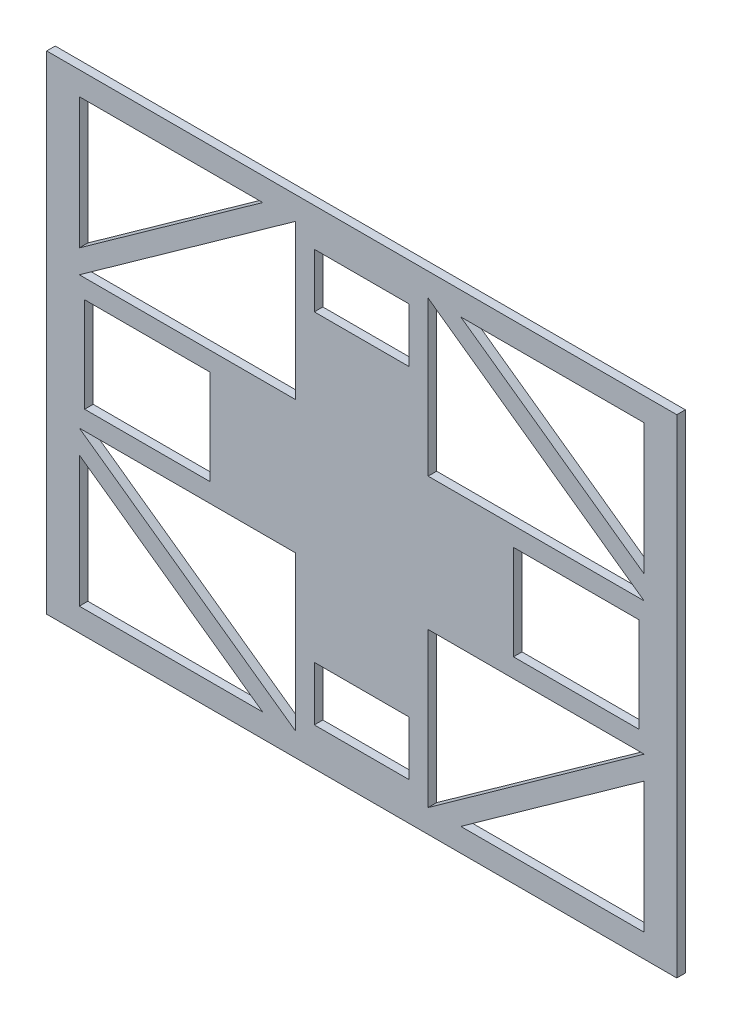
SolidWorks part; units mm, degrees
material "CA"
ref_plane "Ön Düzlem" through (0, 0, 0) normal (0, 0, 1) x (1, 0, 0)
ref_plane "Üst Düzlem" through (0, 0, 0) normal (0, 1, 0) x (1, 0, 0)
ref_plane "Sağ Düzlem" through (0, 0, 0) normal (1, 0, 0) x (0, 0, -1)
sketch "Çizim1" plane through (0, 0, 0) normal (0, 0, 1) x (1, 0, 0)
  line L0 (-35, 128.6) -> (-166.1, 35)
  line L1 (-166.1, -35) -> (166.1, -35)
  line L2 (-166.1, -35) -> (-166.1, 35)
  line L3 (-166.1, 35) -> (166.1, 35)
  line L4 (166.1, -35) -> (166.1, 35)
  line L5 (-166.1, -35) -> (166.1, 35) construction
  line L6 (-166.1, 35) -> (166.1, -35) construction
  line L7 (-35, -128.6) -> (35, -128.6)
  line L8 (-35, -128.6) -> (-35, 128.6)
  line L9 (-35, 128.6) -> (35, 128.6)
  line L10 (35, -128.6) -> (35, 128.6)
  line L11 (-35, -128.6) -> (35, 128.6) construction
  line L12 (-35, 128.6) -> (35, -128.6) construction
  line L13 (-35, -128.6) -> (-166.1, -35)
  line L14 (35, -128.6) -> (166.1, -35)
  line L15 (166.1, 35) -> (35, 128.6)
  line L16 (-148.8901, 35) -> (-35, 116.3129)
  line L17 (-35, -116.3129) -> (-148.8901, -35)
  line L18 (35, -116.3129) -> (148.8901, -35)
  line L19 (35, 116.3129) -> (148.8901, 35)
  line L20 (-35, 25) -> (-146.1, 25)
  line L21 (-146.1, 25) -> (-146.1, -25)
  line L22 (-146.1, -25) -> (-35, -25)
  line L23 (35, 25) -> (146.1, 25)
  line L24 (-25, -25) -> (25, -25)
  line L25 (-25, -25) -> (-25, 25)
  line L26 (-25, 25) -> (25, 25)
  line L27 (25, -25) -> (25, 25)
  line L28 (-25, -25) -> (25, 25) construction
  line L29 (-25, 25) -> (25, -25) construction
  line L30 (146.1, 25) -> (146.1, -25)
  line L31 (146.1, -25) -> (35, -25)
  line L32 (-25, 35) -> (-25, 108.6)
  line L33 (-25, 108.6) -> (25, 108.6)
  line L34 (25, 108.6) -> (25, 35)
  line L35 (-25, -35) -> (-25, -108.6)
  line L36 (-25, -108.6) -> (25, -108.6)
  line L37 (25, -108.6) -> (25, -35)
  line L38 (-166.1, -35) -> (-166.1, -128.6)
  line L39 (-166.1, -128.6) -> (-35, -128.6)
  line L40 (-148.8901, -35) -> (-148.8901, -116.3129)
  line L41 (-148.8901, -116.3129) -> (-35, -116.3129)
  line L42 (166.1, -35) -> (166.1, -128.6)
  line L43 (166.1, -128.6) -> (35, -128.6)
  line L44 (35, -116.3129) -> (148.8901, -116.3129)
  line L45 (148.8901, -116.3129) -> (148.8901, -35)
  line L48 (35, 128.6) -> (166.1, 128.6)
  line L49 (166.1, 128.6) -> (166.1, 35)
  line L50 (-166.1, 35) -> (-166.1, 128.6)
  line L51 (-166.1, 128.6) -> (-35, 128.6)
  line L52 (-148.8901, 35) -> (-148.8901, 116.3129)
  line L53 (-148.8901, 116.3129) -> (-35, 116.3129)
  line L54 (-25, -80) -> (25, -80)
  line L55 (-80, 25) -> (-80, -25)
  line L56 (-25, 80) -> (25, 80)
  line L57 (80, 25) -> (80, -25)
  line L58 (35, 116.3129) -> (148.8901, 116.3129)
  line L59 (148.8901, 116.3129) -> (148.8901, 35)
  point P0 (0, 0)
  point P6 (0, 0)
  point P21 (0, 0)
  dimension "D1" = 70
  dimension "D2" = 332.2
  dimension "D3" = 70
  dimension "D4" = 257.2
  dimension "D5" = 10
  dimension "D6" = 10
  dimension "D7" = 10
  dimension "D8" = 10
  dimension "D9" = 20
  dimension "D10" = 10
  dimension "D11" = 10
  dimension "D12" = 10
  dimension "D13" = 10
  dimension "D14" = 20
  dimension "D15" = 20
  dimension "D16" = 20
  dimension "D17" = 80
  dimension "D18" = 80
  dimension "D19" = 80
  dimension "D20" = 80
extrude "Yükseklik-Ekstrüzyon2" add sketch "Çizim1" against normal blind 4.5
sketch "Çizim2" plane through (0, 0, -4.5) normal (0, 0, -1) x (-1, 0, 0)
  circle A0 centre (0, 0) radius 3
  dimension "D1" = 6
extrude "Yükseklik-Ekstrüzyon3" add sketch "Çizim2" along normal blind 10
sketch "Çizim3" plane through (0, 0, 0) normal (0, 0, 1) x (1, 0, 0)
  line L0 (-166.1, 128.6) -> (166.1, 128.6) construction
  line L1 (-166.1, 128.6) -> (-166.1, -128.6) construction
  line L2 (-166.1, -128.6) -> (166.1, -128.6) construction
  line L4 (161.1, 0) -> (166.1, 0) construction
  line L5 (166.1, -128.6) -> (166.1, 128.6) construction
  line L6 (161.1, 25) -> (166.1, 25)
  line L7 (161.1, -25) -> (166.1, -25)
  line L8 (-161.1, -123.6) -> (161.1, -123.6)
  line L9 (161.1, -123.6) -> (161.1, 123.6)
  line L10 (161.1, 123.6) -> (-161.1, 123.6)
  line L11 (-161.1, 123.6) -> (-161.1, -123.6)
  line L12 (-161.1, -123.6) -> (161.1, -123.6)
  line L13 (161.1, -123.6) -> (161.1, 123.6)
  line L14 (161.1, 123.6) -> (-161.1, 123.6)
  line L15 (-161.1, 123.6) -> (-161.1, -123.6)
  circle A0 centre (164.1, 126.6) radius 1
  circle A1 centre (-164.1, 126.6) radius 1
  circle A2 centre (-164.1, -126.6) radius 1
  circle A3 centre (164.1, -126.6) radius 1
  dimension "D4" = 2
  dimension "D5" = 2
  dimension "D7" = 2
  dimension "D10" = 2
  dimension "D13" = 2
  dimension "D2" = 25
  dimension "D3" = 25
  dimension "D6" = 2
  dimension "D8" = 2
  dimension "D9" = 2
  dimension "D11" = 2
  dimension "D12" = 2
  dimension "D14" = 2
  dimension "D15" = 2
  dimension "D1" = 5
sketch "Çizim4" plane through (0, 0, -4.5) normal (0, 0, -1) x (-1, 0, 0)
  line L1 (-52.5, -2.5) -> (-67.5, -2.5)
  line L2 (-52.5, -2.5) -> (-52.5, 2.5)
  line L3 (-52.5, 2.5) -> (-67.5, 2.5)
  line L4 (-67.5, -2.5) -> (-67.5, 2.5)
  line L5 (-52.5, -2.5) -> (-67.5, 2.5) construction
  line L6 (-52.5, 2.5) -> (-67.5, -2.5) construction
  line L7 (2.5, -67.5) -> (-2.5, -67.5)
  line L8 (2.5, -67.5) -> (2.5, -52.5)
  line L9 (2.5, -52.5) -> (-2.5, -52.5)
  line L10 (-2.5, -67.5) -> (-2.5, -52.5)
  line L11 (2.5, -67.5) -> (-2.5, -52.5) construction
  line L12 (2.5, -52.5) -> (-2.5, -67.5) construction
  point P0 (-60, 0)
  point P8 (0, -60)
  dimension "D1" = 5
  dimension "D2" = 15
  dimension "D3" = 60
  dimension "D4" = 5
  dimension "D5" = 15
  dimension "D6" = 60
extrude "Yükseklik-Ekstrüzyon5" add sketch "Çizim4" along normal blind 10
sketch "Çizim5" plane through (0, -2.5, 0) normal (0, -1, 0) x (1, 0, 0)
  line L0 (67.5, -4.5) -> (52.5, -4.5) construction
  line L1 (52.5, -14.5) -> (52.5, -4.5) construction
  circle A0 centre (60, -9.5) radius 2
  circle A1 centre (60, -18.5) radius 2
  dimension "D1" = 4
  dimension "D4" = 4
  dimension "D2" = 5
  dimension "D3" = 7.5
  dimension "D5" = 7.5
  dimension "D6" = 14
sketch "Çizim6" plane through (2.5, 0, 0) normal (1, 0, 0) x (0, 0, -1)
  line L0 (4.5, -128.6) -> (4.5, 128.6) construction
  line L1 (14.5, -67.5) -> (4.5, -67.5) construction
  line L2 (4.5, -52.5) -> (4.5, -67.5) construction
  circle A0 centre (9.5, -60) radius 2
  circle A1 centre (18.5, -60) radius 2
  dimension "D1" = 4
  dimension "D2" = 4
  dimension "D3" = 5
  dimension "D4" = 7.5
  dimension "D5" = 7.5
  dimension "D6" = 14
extrude "Kes-Ekstrüzyon1" cut sketch "Çizim5" against normal through all
extrude "Kes-Ekstrüzyon2" cut sketch "Çizim6" against normal through all
ref_point "Nokta1"
